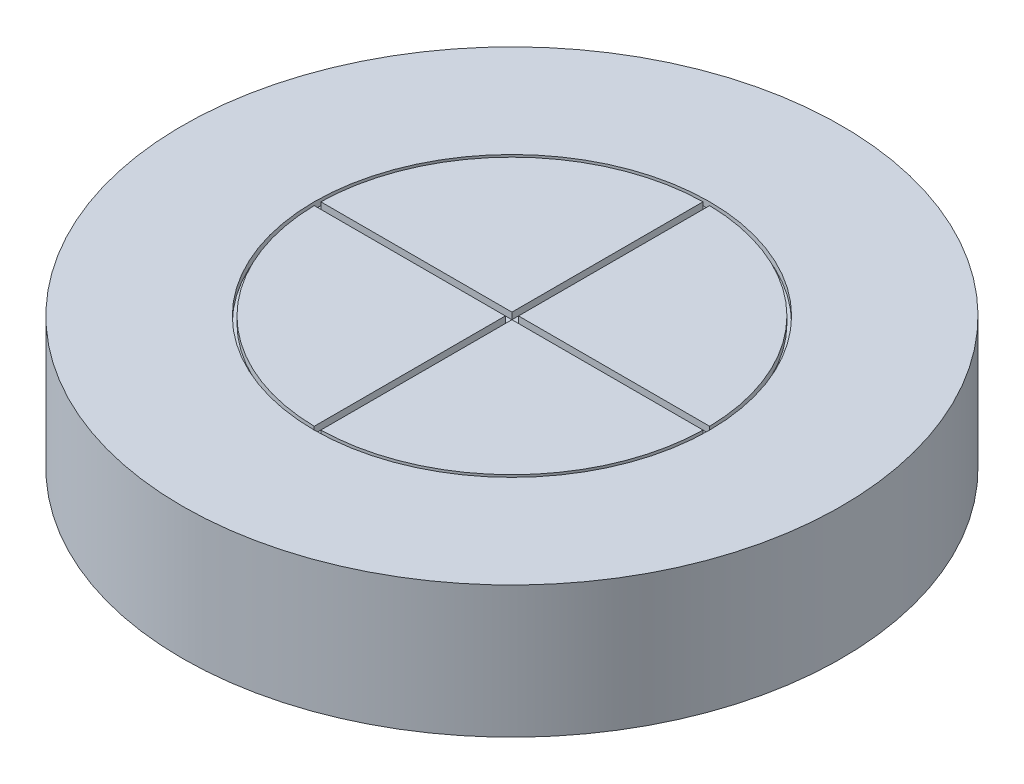
SolidWorks part; units mm, degrees
ref_plane "Front Plane" through (0, 0, 0) normal (0, 0, 1) x (1, 0, 0)
ref_plane "Top Plane" through (0, 0, 0) normal (0, 1, 0) x (1, 0, 0)
ref_plane "Right Plane" through (0, 0, 0) normal (1, 0, 0) x (0, 0, -1)
sketch "Sketch1" plane through (0, 0, 0) normal (0, 1, 0) x (1, 0, 0)
  line L0 (-0.5, 0.5) -> (-0.5, 29.4958)
  line L1 (0.5, -0.0085) -> (0.5, 0.0085)
  line L2 (-0.5, -29.4958) -> (-0.5, -0.5)
  line L3 (0.5, 0.5) -> (0.5, 29.4958)
  line L4 (0.5, -29.4958) -> (0.5, -0.5)
  line L5 (-0.5, -29.4958) -> (0.5, 29.4958) construction
  line L6 (-0.5, 29.4958) -> (0.5, -29.4958) construction
  line L7 (29.4958, 0.5) -> (0.5, 0.5)
  line L8 (0.0085, 0.5) -> (-0.0085, 0.5)
  line L9 (29.4958, -0.5) -> (0.5, -0.5)
  line L11 (29.4958, 0.5) -> (-29.4958, -0.5) construction
  line L12 (29.4958, -0.5) -> (-29.4958, 0.5) construction
  line L13 (-0.5, 0.5) -> (-29.4958, 0.5)
  line L14 (-0.5, -0.0085) -> (-0.5, 0.0085)
  line L15 (-0.5, -0.5) -> (-29.4958, -0.5)
  line L16 (0.0085, -0.5) -> (-0.0085, -0.5)
  circle A0 centre (0, 0) radius 50
  circle A1 centre (0, 0) radius 30
  arc A2 (-0.5, 29.4958) -> (-29.4958, 0.5) centre (0, 0) ccw
  arc A3 (29.4958, 0.5) -> (0.5, 29.4958) centre (0, 0) ccw
  arc A4 (0.5, -29.4958) -> (29.4958, -0.5) centre (0, 0) ccw
  arc A5 (-29.4958, -0.5) -> (-0.5, -29.4958) centre (0, 0) ccw
ref_plane "Plane1" through (0, 0, 0) normal (0, 1, 0) x (1, 0, 0)
sketch "Sketch2" plane through (0, 0, 0) normal (0, 1, 0) x (1, 0, 0)
  circle A0 centre (0, 0) radius 50
  point P3 (-50, 0)
extrude "Boss-Extrude2" add sketch "Sketch2" against normal blind 20
extrude "Cut-Extrude1" cut sketch "Sketch1" against normal blind 1
ref_plane "Plane2" through (-50, 0, 0) normal (-1, 0, 0) x (0, 0, 1)
ref_plane "Plane3" through (0, 0, 0) normal (0, 1, 0) x (1, 0, 0)
sketch "Sketch4" plane through (0, 0, 0) normal (0, 1, 0) x (1, 0, 0)
  point P0 (0, 0)
hole_wizard "#60 (0.04) Diameter Hole1" positions "3DSketch2" profile "Sketch5" hole size "#60" standard "ANSI Inch"
sketch3d "3DSketch2"
  point P0 (0, 0, 0)
  point P3 (0, -1, 0)
sketch "Sketch5" plane through (0, -1, 0) normal (1, 0, 0) x (0, 0, 1)
  line L0 (0, 0) -> (0, 10.3052)
  line L1 (0, 10.3052) -> (0.508, 10)
  line L2 (0.508, 10) -> (0.508, 0)
  line L5 (0.508, 0) -> (0, 0)
  line L10 (0, 10.3052) -> (-0.508, 10) construction
  line L11 (0, -6.35) -> (0, 107.95) construction
  dimension "Hole Dia." = 1.016
  dimension "Hole Depth" = 10
  dimension "Drill Angle" = 118
sketch "Sketch6" plane through (-50, 0, 0) normal (-1, 0, 0) x (0, 0, 1)
  point P3 (0, -9.8327)
hole_wizard "#2 (0.221) Diameter Hole1" positions "3DSketch3" profile "Sketch7" hole size "#2" standard "ANSI Inch"
sketch3d "3DSketch3"
  point P0 (-50, -9.8327, 0)
  point P3 (-50, -9.8327, 0)
sketch "Sketch7" plane through (-50, -9.8327, 0) normal (0, 1, 0) x (0, 0, 1)
  line L0 (0, 0) -> (0, 56.6864)
  line L1 (0, 56.6864) -> (2.8067, 55)
  line L2 (2.8067, 55) -> (2.8067, 0)
  line L5 (2.8067, 0) -> (0, 0)
  line L10 (0, 56.6864) -> (-2.8067, 55) construction
  line L11 (0, -6.35) -> (0, 107.95) construction
  dimension "Hole Dia." = 5.6134
  dimension "Hole Depth" = 55
  dimension "Drill Angle" = 118
sketch "Sketch8" plane through (0, 0, 0) normal (0, 1, 0) x (1, 0, 0)
  circle A0 centre (0, 0) radius 50
ref_plane "Plane4" through (0, -20, 0) normal (0, -1, 0) x (-1, 0, 0)
sketch "Sketch9" plane through (0, -20, 0) normal (0, -1, 0) x (-1, 0, 0)
  line L0 (-5, 0) -> (5, 0)
  arc A0 (5, 0) -> (-5, 0) centre (0, 0) ccw
revolve "Cut-Revolve1" cut sketch "Sketch9" angle 360 about L0
